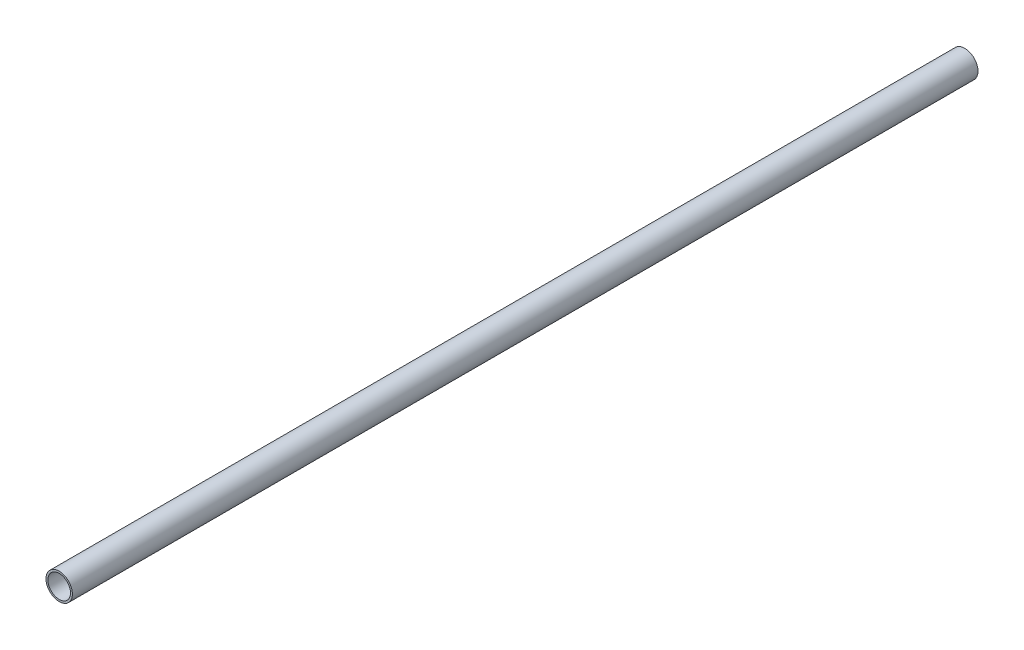
SolidWorks part; units mm, degrees
material "PVC Rigid"
ref_plane "Front Plane" through (0, 0, 0) normal (0, 0, 1) x (1, 0, 0)
ref_plane "Top Plane" through (0, 0, 0) normal (0, 1, 0) x (1, 0, 0)
ref_plane "Right Plane" through (0, 0, 0) normal (1, 0, 0) x (0, 0, -1)
sketch "Sketch1" plane through (0, 0, 0) normal (0, 0, 1) x (1, 0, 0)
  circle A0 centre (0, 0) radius 44.45
  circle A1 centre (0, 0) radius 38.1
  dimension "D1" = 88.9
  dimension "D2" = 76.2
extrude "Boss-Extrude1" add sketch "Sketch1" along normal mid plane 3048
